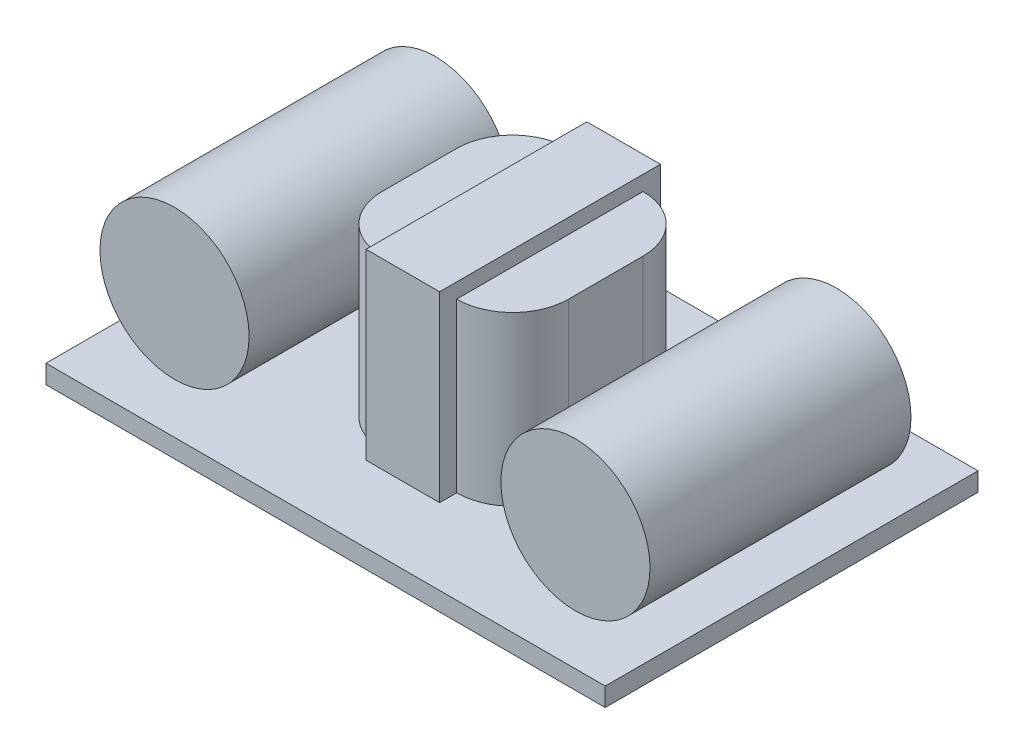
SolidWorks part; units mm, degrees
ref_plane "Front Plane" through (0, 0, 0) normal (0, 0, 1) x (1, 0, 0)
ref_plane "Top Plane" through (0, 0, 0) normal (0, 1, 0) x (1, 0, 0)
ref_plane "Right Plane" through (0, 0, 0) normal (1, 0, 0) x (0, 0, -1)
sketch "Sketch1" plane through (0, 0, 0) normal (0, 1, 0) x (1, 0, 0)
  line L1 (-13.0929, 10.4279) -> (16.9071, 10.4279)
  line L2 (-13.0929, 10.4279) -> (-13.0929, -9.5721)
  line L3 (-13.0929, -9.5721) -> (16.9071, -9.5721)
  line L4 (16.9071, 10.4279) -> (16.9071, -9.5721)
  dimension "D1" = 30
  dimension "D2" = 20
extrude "Boss-Extrude1" add sketch "Sketch1" along normal blind 1
sketch "Sketch3" plane through (0, 0, 0) normal (0, 0, 1) x (1, 0, 0)
  circle A0 centre (-8.7703, 5.1202) radius 4
  circle A1 centre (12.739, 5.1202) radius 4
  dimension "D1" = 8
  dimension "D2" = 8
extrude "Boss-Extrude2" add sketch "Sketch3" along normal mid plane 14 separate body
sketch "Sketch4" plane through (0, 0, 0) normal (0, 1, 0) x (1, 0, 0)
  line L1 (-3.053, 5.4189) -> (6.947, 5.4189)
  line L2 (-3.053, 5.4189) -> (-3.053, -4.5811)
  line L3 (-3.053, -4.5811) -> (6.947, -4.5811)
  line L4 (6.947, 5.4189) -> (6.947, -4.5811)
  dimension "D1" = 10
  dimension "D2" = 10
extrude "Boss-Extrude3" add sketch "Sketch4" along normal blind 10
fillet "Fillet1" radius 3 4 edges at (6.947, 5.5, -5.4189) (-3.053, 5.5, -5.4189) (-3.053, 5.5, 4.5811) (6.947, 5.5, 4.5811)
sketch "Sketch5" plane through (0, 0, 0) normal (1, 0, 0) x (0, 0, -1)
  line L0 (-9.5721, 1) -> (10.4279, 1) construction
  line L1 (-5.4954, 1) -> (6.3512, 1)
  line L2 (-5.4954, 1) -> (-5.4954, 10.7997)
  line L3 (-5.4954, 10.7997) -> (6.3512, 10.7997)
  line L4 (6.3512, 1) -> (6.3512, 10.7997)
extrude "Boss-Extrude4" add sketch "Sketch5" along normal offset from surface (3.947 mm away) 3 up to face at (6.947, 5.5, -0.4189)
